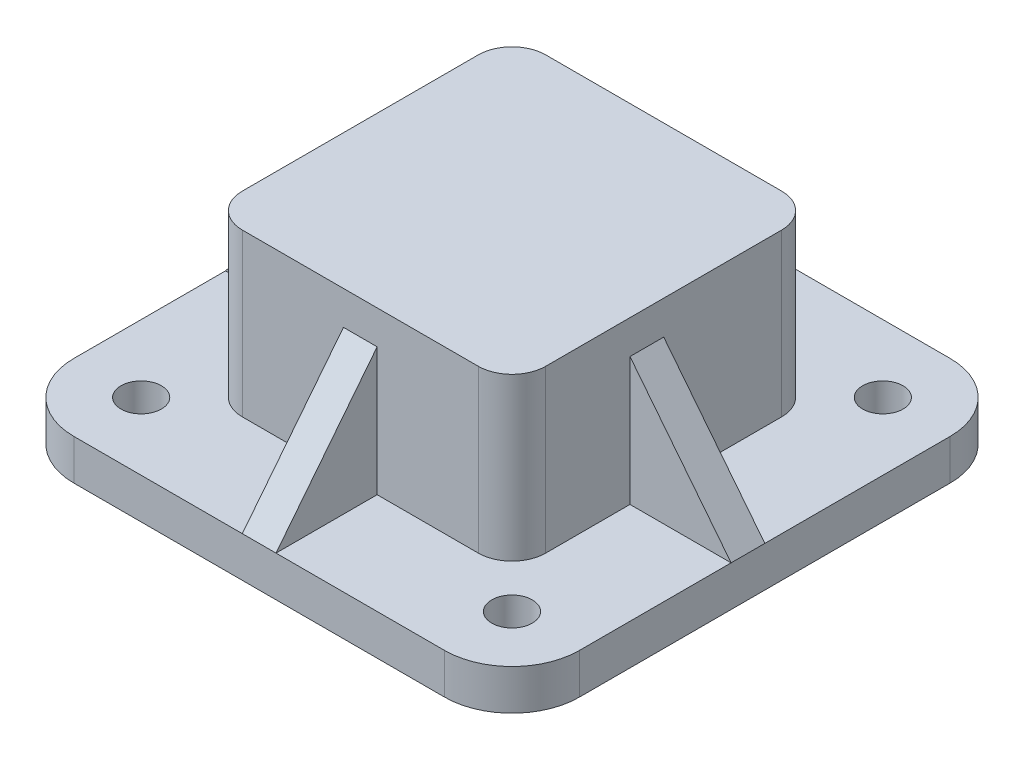
SolidWorks part; units mm, degrees
ref_plane "Front Plane" through (0, 0, 0) normal (0, 0, 1) x (1, 0, 0)
ref_plane "Top Plane" through (0, 0, 0) normal (0, 1, 0) x (1, 0, 0)
ref_plane "Right Plane" through (0, 0, 0) normal (1, 0, 0) x (0, 0, -1)
sketch "Sketch1" plane through (0, 0, 0) normal (0, 1, 0) x (1, 0, 0)
  line L1 (-55, 75) -> (55, 75)
  line L2 (-75, 55) -> (-75, -55)
  line L3 (-55, -75) -> (55, -75)
  line L4 (75, 55) -> (75, -55)
  line L5 (-75, 75) -> (75, -75) construction
  line L6 (-75, -75) -> (75, 75) construction
  arc A0 (75, 55) -> (55, 75) centre (55, 55) ccw
  arc A1 (55, -75) -> (75, -55) centre (55, -55) ccw
  arc A2 (-55, -75) -> (-75, -55) centre (-55, -55) cw
  arc A3 (-75, 55) -> (-55, 75) centre (-55, 55) cw
  circle A4 centre (-55, 55) radius 6
  circle A5 centre (-55, -55) radius 6
  circle A6 centre (55, -55) radius 6
  circle A7 centre (55, 55) radius 6
  point P0 (0, 0)
  dimension "D3" = 20
  dimension "D4" = 12
  dimension "D5" = 12
  dimension "D6" = 12
  dimension "D7" = 12
  dimension "D1" = 150
  dimension "D2" = 150
extrude "Boss-Extrude2" add sketch "Sketch1" along normal blind 12
sketch "Sketch2" plane through (0, 12, 0) normal (0, 1, 0) x (1, 0, 0)
  line L1 (-35, 45) -> (35, 45)
  line L2 (-45, 35) -> (-45, -35)
  line L3 (-35, -45) -> (35, -45)
  line L4 (45, 35) -> (45, -35)
  line L5 (-45, 45) -> (45, -45) construction
  line L6 (-45, -45) -> (45, 45) construction
  arc A0 (45, 35) -> (35, 45) centre (35, 35) ccw
  arc A1 (35, -45) -> (45, -35) centre (35, -35) ccw
  arc A2 (-35, -45) -> (-45, -35) centre (-35, -35) cw
  arc A3 (-45, 35) -> (-35, 45) centre (-35, 35) cw
  point P0 (0, 0)
  dimension "D3" = 10
  dimension "D1" = 90
  dimension "D2" = 90
extrude "Boss-Extrude3" add sketch "Sketch2" along normal blind 48 contours L2 A2 L3 A1 L4 A0 L1 A3
sketch "Sketch3" plane through (0, 0, 0) normal (1, 0, 0) x (0, 0, -1)
  line L0 (45, 50) -> (45, 12)
  line L1 (45, 60) -> (45, 12) construction
  line L2 (45, 12) -> (75, 12)
  line L3 (75, 12) -> (45, 50)
  line L5 (-45, 12) -> (-75, 12)
  line L6 (-75, 12) -> (-45, 50)
  line L7 (-45, 50) -> (-45, 12)
  dimension "D1" = 10
  dimension "D2" = 48
sketch "Sketch6" plane through (0, 0, 0) normal (0, 0, 1) x (1, 0, 0)
  line L0 (45, 50) -> (75, 12)
  line L1 (45, 60) -> (45, 12) construction
  line L2 (75, 12) -> (45, 12)
  line L3 (45, 12) -> (45, 50)
  line L4 (-45, 50) -> (-45, 12)
  line L5 (-45, 60) -> (-45, 12) construction
  line L6 (-45, 12) -> (-75, 12)
  line L7 (-75, 12) -> (-45, 50)
  dimension "D1" = 10
  dimension "D2" = 10
extrude "Boss-Extrude5" add sketch "Sketch3" along normal mid plane 10
extrude "Boss-Extrude6" add sketch "Sketch6" along normal blind 10 contours L0 L2 L3 | L7 L4 L6
